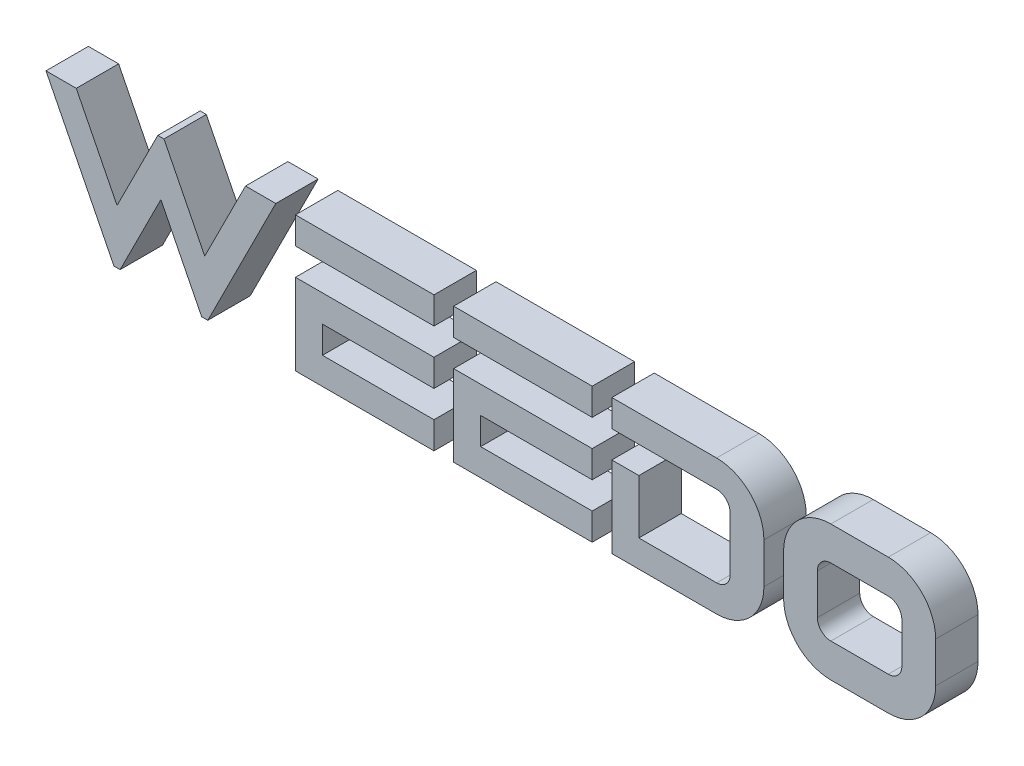
SolidWorks part; units mm, degrees
ref_plane "前视" through (0, 0, 0) normal (0, 0, 1) x (1, 0, 0)
ref_plane "上视" through (0, 0, 0) normal (0, 1, 0) x (1, 0, 0)
ref_plane "右视" through (0, 0, 0) normal (1, 0, 0) x (0, 0, -1)
sketch "草图1" plane through (0, 0, 0) normal (0, 0, 1) x (1, 0, 0)
  line L0 (-50.9609, 11.1265) -> (-57.3772, -1.6335)
  line L1 (-19.2349, 11.1265) -> (-9.3459, 11.1265)
  line L2 (-21.0909, -1.6335) -> (-34.1699, -1.6335)
  line L3 (-57.3772, -1.6335) -> (-57.9571, -1.6335)
  line L4 (-66.2366, -1.6335) -> (-72.6529, 11.1265)
  line L5 (-19.2349, 6.0225) -> (-16.6829, 6.0225)
  line L6 (-62.0969, 11.1265) -> (-61.517, 11.1265)
  line L7 (-19.2349, -1.6335) -> (-19.2349, 6.0225)
  line L8 (-19.2349, 8.5745) -> (-19.2349, 11.1265)
  line L9 (-49.1049, 11.1265) -> (-36.0259, 11.1265)
  line L10 (-72.6529, 11.1265) -> (-69.7964, 11.1265)
  line L11 (-69.7964, 11.1265) -> (-65.9467, 3.4705)
  line L12 (-61.517, 11.1265) -> (-57.6672, 3.4705)
  line L13 (-4.8799, 6.6605) -> (-4.8799, 2.8325)
  line L14 (-16.6829, 0.9185) -> (-9.3459, 0.9185)
  line L15 (-9.3459, 8.5745) -> (-19.2349, 8.5745)
  line L16 (-57.9571, -1.6335) -> (-61.8069, 6.0225)
  line L17 (-65.9467, 3.4705) -> (-62.0969, 11.1265)
  line L18 (-34.1699, -1.6335) -> (-34.1699, 6.0225)
  line L19 (-36.0259, 3.4705) -> (-46.5529, 3.4705)
  line L20 (-49.1049, 6.0225) -> (-36.0259, 6.0225)
  line L21 (-53.8174, 11.1265) -> (-50.9609, 11.1265)
  line L22 (-8.0699, 2.1945) -> (-8.0699, 7.2985)
  line L23 (1.4421, 1.5565) -> (6.8651, 1.5565)
  line L24 (-46.5529, 3.4705) -> (-46.5529, 0.9185)
  line L25 (-21.0909, 11.1265) -> (-21.0909, 8.5745)
  line L26 (-49.1049, -1.6335) -> (-49.1049, 6.0225)
  line L27 (-65.6567, -1.6335) -> (-66.2366, -1.6335)
  line L28 (-3.0239, 2.8325) -> (-3.0239, 6.6605)
  line L29 (0.1661, 6.6605) -> (0.1661, 2.8325)
  line L30 (-31.6179, 3.4705) -> (-31.6179, 0.9185)
  line L31 (-36.0259, 11.1265) -> (-36.0259, 8.5745)
  line L32 (-36.0259, -1.6335) -> (-49.1049, -1.6335)
  line L33 (6.8651, -1.6335) -> (1.4421, -1.6335)
  line L34 (-16.6829, 6.0225) -> (-16.6829, 0.9185)
  line L35 (-61.8069, 6.0225) -> (-65.6567, -1.6335)
  line L36 (-21.0909, 0.9185) -> (-21.0909, -1.6335)
  line L37 (6.8651, 7.9365) -> (1.4421, 7.9365)
  line L38 (-34.1699, 11.1265) -> (-21.0909, 11.1265)
  line L39 (-49.1049, 8.5745) -> (-49.1049, 11.1265)
  line L40 (-21.0909, 8.5745) -> (-34.1699, 8.5745)
  line L41 (11.3311, 6.6605) -> (11.3311, 2.8325)
  line L42 (-57.6672, 3.4705) -> (-53.8174, 11.1265)
  line L43 (-36.0259, 0.9185) -> (-36.0259, -1.6335)
  line L44 (-21.0909, 6.0225) -> (-21.0909, 3.4705)
  line L45 (-31.6179, 0.9185) -> (-21.0909, 0.9185)
  line L46 (-65.9467, 3.4705) -> (-60.6856, 3.4705) construction
  line L47 (-36.0259, 6.0225) -> (-36.0259, 3.4705)
  line L48 (-34.1699, 8.5745) -> (-34.1699, 11.1265)
  line L49 (8.1411, 2.8325) -> (8.1411, 6.6605)
  line L50 (-9.3459, -1.6335) -> (-19.2349, -1.6335)
  line L51 (1.4421, 11.1265) -> (6.8651, 11.1265)
  line L52 (-36.0259, 8.5745) -> (-49.1049, 8.5745)
  line L53 (-34.1699, 6.0225) -> (-21.0909, 6.0225)
  line L54 (-46.5529, 0.9185) -> (-36.0259, 0.9185)
  line L55 (-21.0909, 3.4705) -> (-31.6179, 3.4705)
  arc A0 (-8.0699, 7.2985) -> (-9.3459, 8.5745) centre (-9.3459, 7.2985) ccw
  arc A1 (-8.0699, 2.1945) -> (-9.3459, 0.9185) centre (-9.3459, 2.1945) cw
  arc A2 (8.1411, 6.6605) -> (6.8651, 7.9365) centre (6.8651, 6.6605) ccw
  arc A3 (-3.0239, 2.8325) -> (1.4421, -1.6335) centre (1.4421, 2.8325) ccw
  arc A4 (6.8651, 1.5565) -> (8.1411, 2.8325) centre (6.8651, 2.8325) ccw
  arc A5 (-4.8799, 2.8325) -> (-9.3459, -1.6335) centre (-9.3459, 2.8325) cw
  arc A6 (11.3311, 6.6605) -> (6.8651, 11.1265) centre (6.8651, 6.6605) ccw
  arc A7 (-3.0239, 6.6605) -> (1.4421, 11.1265) centre (1.4421, 6.6605) cw
  arc A8 (-4.8799, 6.6605) -> (-9.3459, 11.1265) centre (-9.3459, 6.6605) ccw
  arc A9 (0.1661, 6.6605) -> (1.4421, 7.9365) centre (1.4421, 6.6605) cw
  arc A10 (0.1661, 2.8325) -> (1.4421, 1.5565) centre (1.4421, 2.8325) ccw
  arc A11 (6.8651, -1.6335) -> (11.3311, 2.8325) centre (6.8651, 2.8325) ccw
extrude "凸台-拉伸1" add sketch "草图1" along normal blind 4
